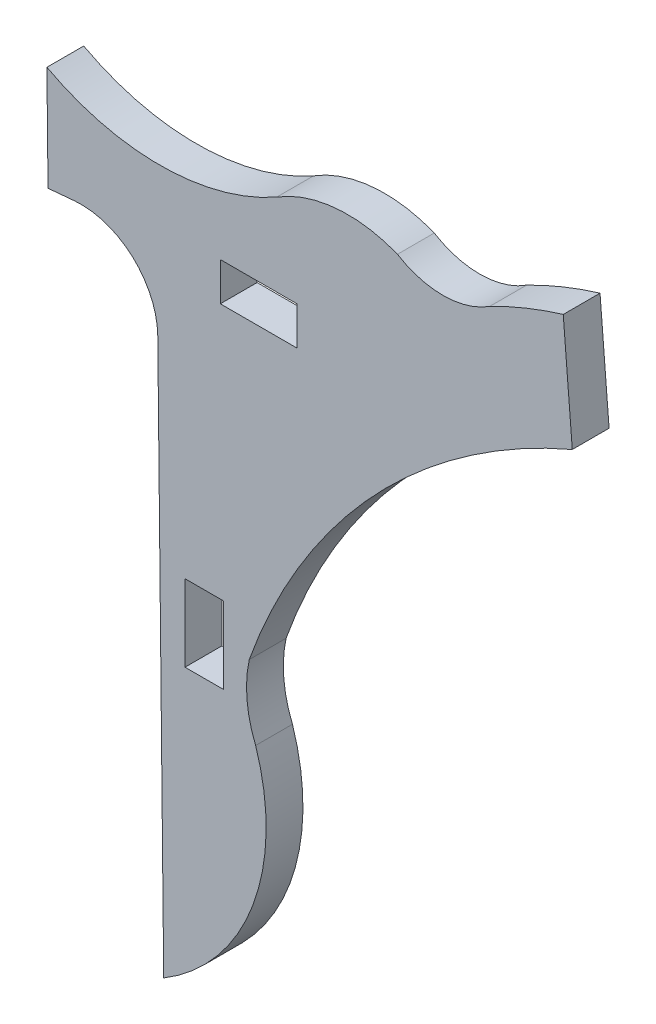
SolidWorks part; units mm, degrees
ref_plane "Front Plane" through (0, 0, 0) normal (0, 0, 1) x (1, 0, 0)
ref_plane "Top Plane" through (0, 0, 0) normal (0, 1, 0) x (1, 0, 0)
ref_plane "Right Plane" through (0, 0, 0) normal (1, 0, 0) x (0, 0, -1)
sketch "Sketch1" plane through (0, 0, 0) normal (0, 0, 1) x (1, 0, 0)
  line L1 (-79.087, 67.6132) -> (-79.4619, 72.2694)
  line L3 (-96.004, 40.2036) -> (-96.2496, 63.0959)
  line L4 (-79.4619, 72.2694) -> (-79.087, 67.6132)
  line L5 (-99.7104, 66.224) -> (-100.7943, 66.1259)
  line L7 (-100.7943, 66.1259) -> (-100.8407, 70.4433)
  line L8 (-90.4857, 65.551) -> (-90.4857, 67.1385)
  line L9 (-90.4857, 67.1385) -> (-93.6607, 67.1385)
  line L10 (-93.6607, 67.1385) -> (-93.6607, 65.551)
  line L11 (-93.6607, 65.551) -> (-90.4857, 65.551)
  line L12 (-95.1232, 54.9631) -> (-93.5357, 54.9631)
  line L13 (-93.5357, 54.9631) -> (-93.5357, 51.7881)
  line L14 (-93.5357, 51.7881) -> (-95.1232, 51.7881)
  line L15 (-95.1232, 51.7881) -> (-95.1232, 54.9631)
  arc A0 (-96.3158, 69.2706) -> (-91.325, 70.5454) centre (-96.1754, 79.1283) ccw
  arc A1 (-91.325, 70.5454) -> (-86.3252, 70.9959) centre (-88.3824, 65.8565) cw
  arc A2 (-86.3252, 70.9959) -> (-82.5034, 71.0369) centre (-84.4467, 74.0347) ccw
  arc A3 (-82.5034, 71.0369) -> (-79.4619, 72.2694) centre (-74.2277, 54.9842) cw
  arc A4 (-79.087, 67.6132) -> (-92.4626, 53.3929) centre (-69.4918, 45.1872) ccw
  arc A5 (-92.4626, 53.3929) -> (-92.1981, 50.4443) centre (-87.6252, 52.3407) ccw
  arc A6 (-99.7104, 66.224) -> (-96.2496, 63.0959) centre (-99.4244, 63.0619) cw
  arc A8 (-100.8407, 70.4433) -> (-96.3158, 69.2706) centre (-96.1754, 79.1283) ccw
  arc A10 (-92.1981, 50.4443) -> (-96.004, 40.2036) centre (-100.5338, 47.7147) cw
  dimension "D1" = 3.175
extrude "Boss-Extrude1" add sketch "Sketch1" along normal blind 1.524
